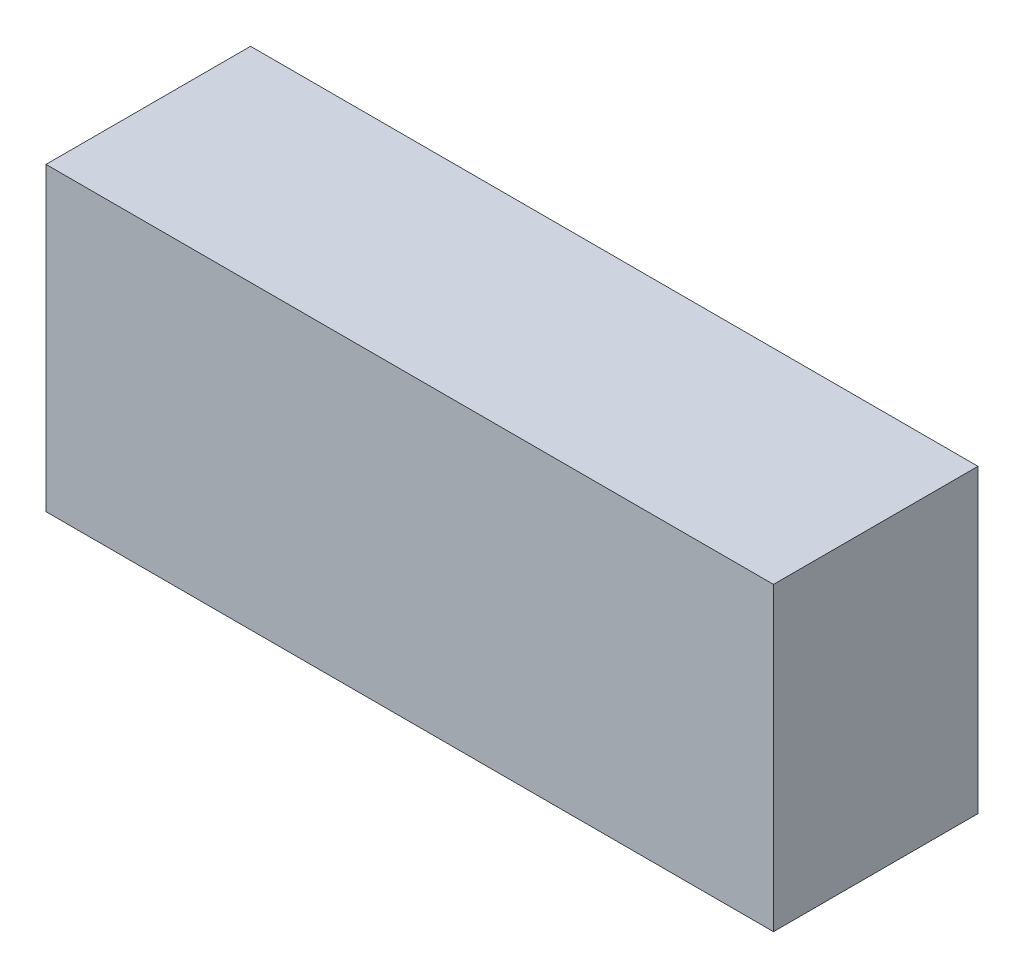
SolidWorks part; units mm, degrees
ref_plane "Front Plane" through (0, 0, 0) normal (0, 0, 1) x (1, 0, 0)
ref_plane "Top Plane" through (0, 0, 0) normal (0, 1, 0) x (1, 0, 0)
ref_plane "Right Plane" through (0, 0, 0) normal (1, 0, 0) x (0, 0, -1)
sketch "Sketch1" plane through (0, 0, 0) normal (0, 0, 1) x (1, 0, 0)
  line L1 (21.5, -8.89) -> (-21.5, -8.89)
  line L2 (21.5, -8.89) -> (21.5, 8.89)
  line L3 (21.5, 8.89) -> (-21.5, 8.89)
  line L4 (-21.5, -8.89) -> (-21.5, 8.89)
  line L5 (21.5, -8.89) -> (-21.5, 8.89) construction
  line L6 (21.5, 8.89) -> (-21.5, -8.89) construction
  point P0 (0, 0)
  dimension "D1" = 43
  dimension "D2" = 17.78
extrude "Boss-Extrude1" add sketch "Sketch1" along normal blind 12.09
